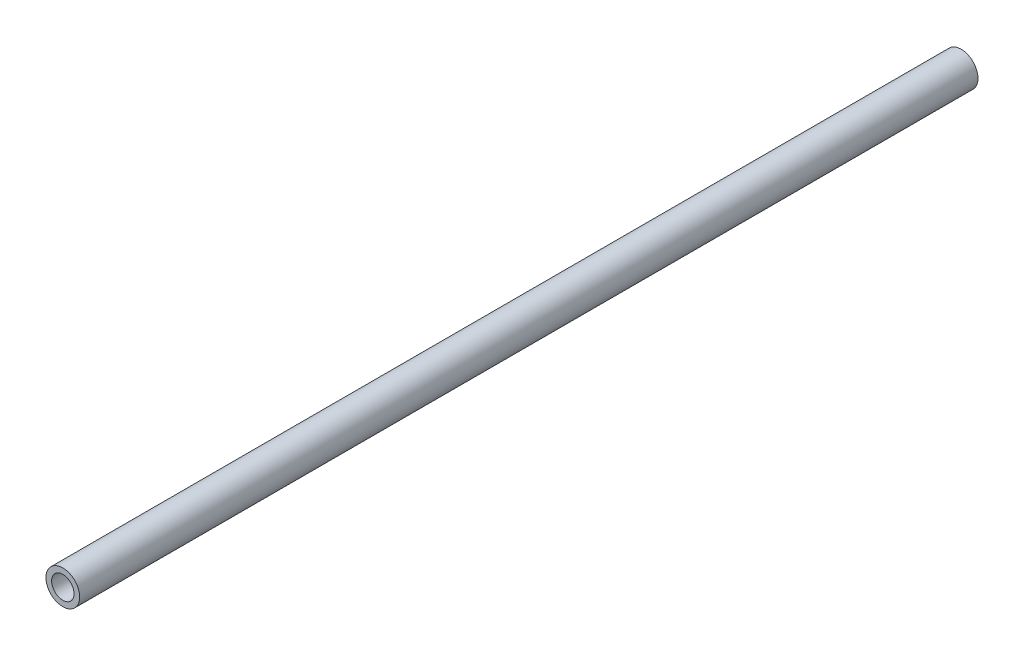
SolidWorks part; units mm, degrees
material "PVC Rigid"
ref_plane "Front Plane" through (0, 0, 0) normal (0, 0, 1) x (1, 0, 0)
ref_plane "Top Plane" through (0, 0, 0) normal (0, 1, 0) x (1, 0, 0)
ref_plane "Right Plane" through (0, 0, 0) normal (1, 0, 0) x (0, 0, -1)
sketch "Sketch1" plane through (0, 0, 0) normal (0, 0, 1) x (1, 0, 0)
  circle A0 centre (0, 0) radius 7.62
  circle A2 centre (0, 0) radius 5.08
  dimension "D1" = 15.24
  dimension "D2" = 10.16
extrude "Boss-Extrude1" add sketch "Sketch1" along normal blind 406.4
